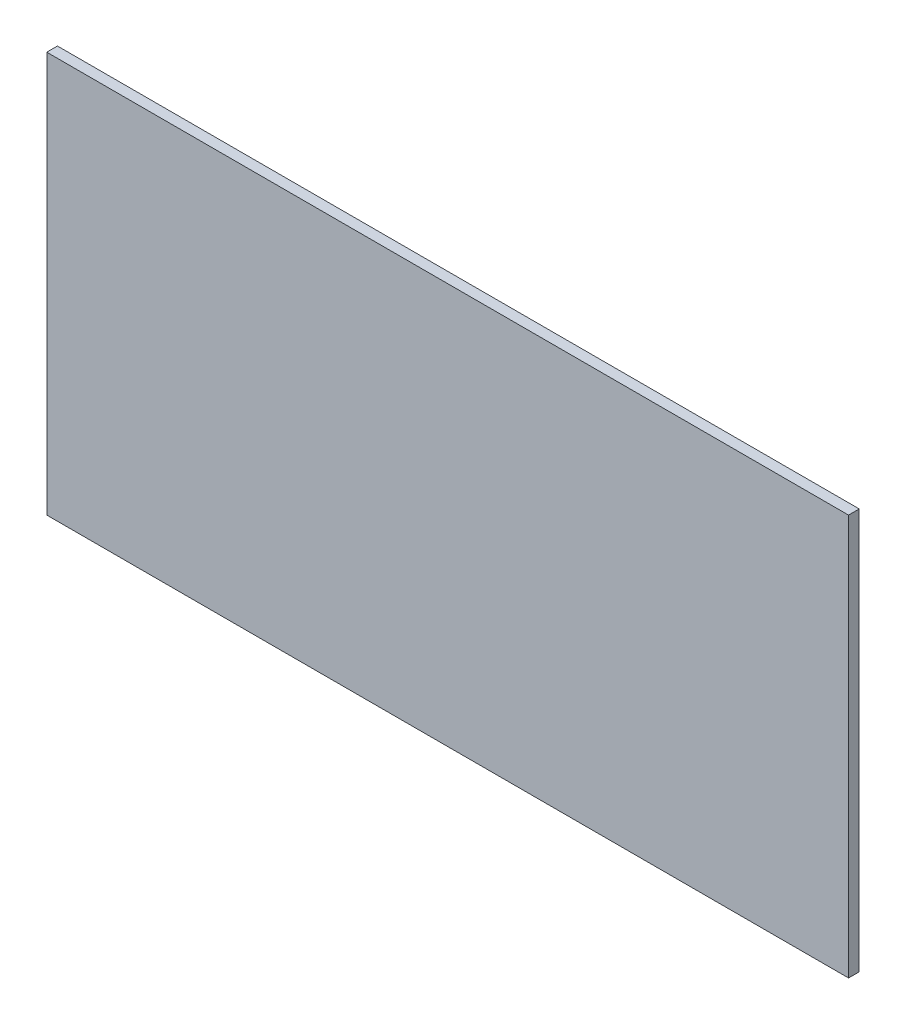
SolidWorks part; units mm, degrees
ref_plane "Front Plane" through (0, 0, 0) normal (0, 0, 1) x (1, 0, 0)
ref_plane "Top Plane" through (0, 0, 0) normal (0, 1, 0) x (1, 0, 0)
ref_plane "Right Plane" through (0, 0, 0) normal (1, 0, 0) x (0, 0, -1)
sketch "Sketch2" plane through (0, 0, 0) normal (0, 0, 1) x (1, 0, 0)
  line L1 (-450, -225) -> (450, -225)
  line L2 (-450, -225) -> (-450, 225)
  line L3 (-450, 225) -> (450, 225)
  line L4 (450, -225) -> (450, 225)
  line L5 (-450, -225) -> (450, 225) construction
  line L6 (-450, 225) -> (450, -225) construction
  point P1 (0, 0)
  dimension "D1" = 450
  dimension "D2" = 900
extrude "Boss-Extrude1" add sketch "Sketch2" along normal blind 12
